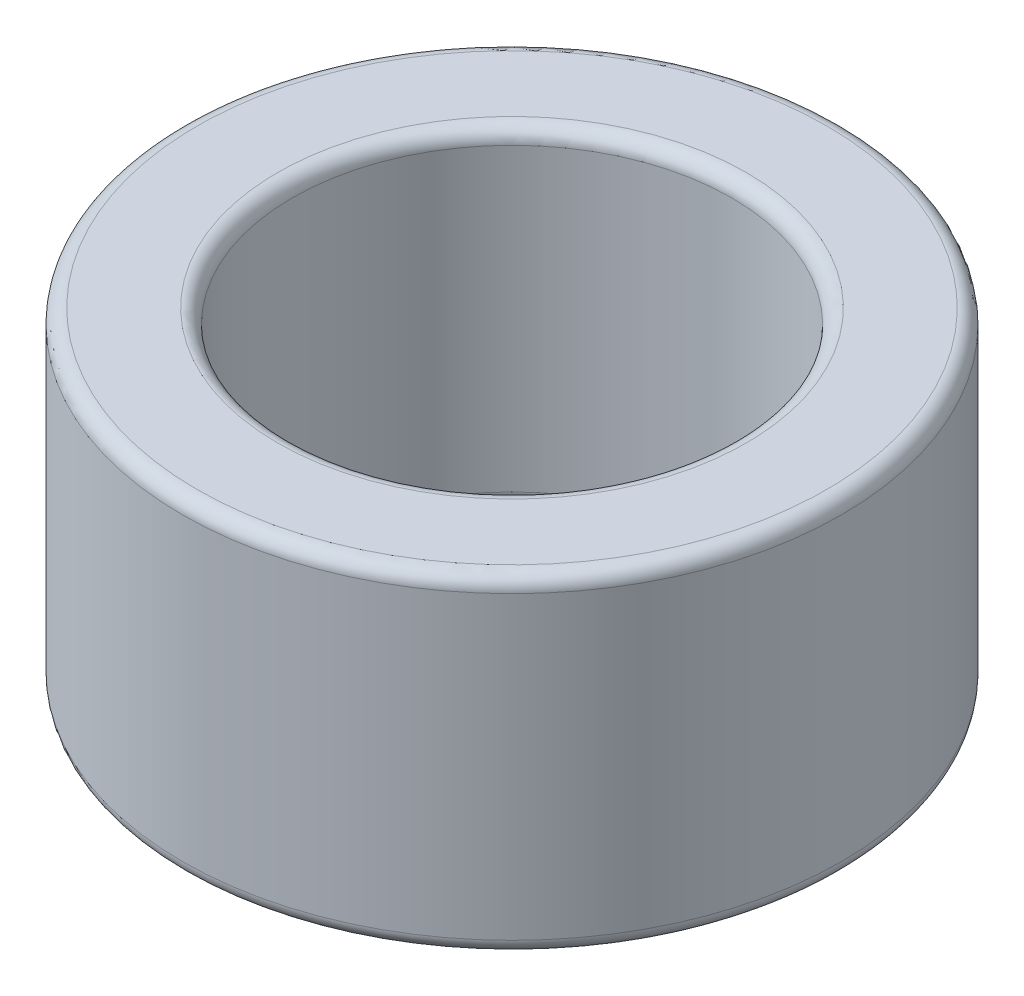
SolidWorks part; units mm, degrees
ref_plane "前视基准面" through (0, 0, 0) normal (0, 0, 1) x (1, 0, 0)
ref_plane "上视基准面" through (0, 0, 0) normal (0, 1, 0) x (1, 0, 0)
ref_plane "右视基准面" through (0, 0, 0) normal (1, 0, 0) x (0, 0, -1)
sketch "草图1" plane through (0, 0, 0) normal (0, 1, 0) x (1, 0, 0)
  circle A0 centre (0, 0) radius 22.5
  circle A1 centre (0, 0) radius 15
  dimension "D1" = 45
  dimension "D2" = 30
extrude "凸台-拉伸1" add sketch "草图1" along normal blind 22.5
fillet "圆角1" radius 1 1 edges at (0, 22.5, 22.5)
fillet "圆角2" radius 1 3 edges at (0, 22.5, 15) (0, 0, 15) (0, 0, 22.5)
